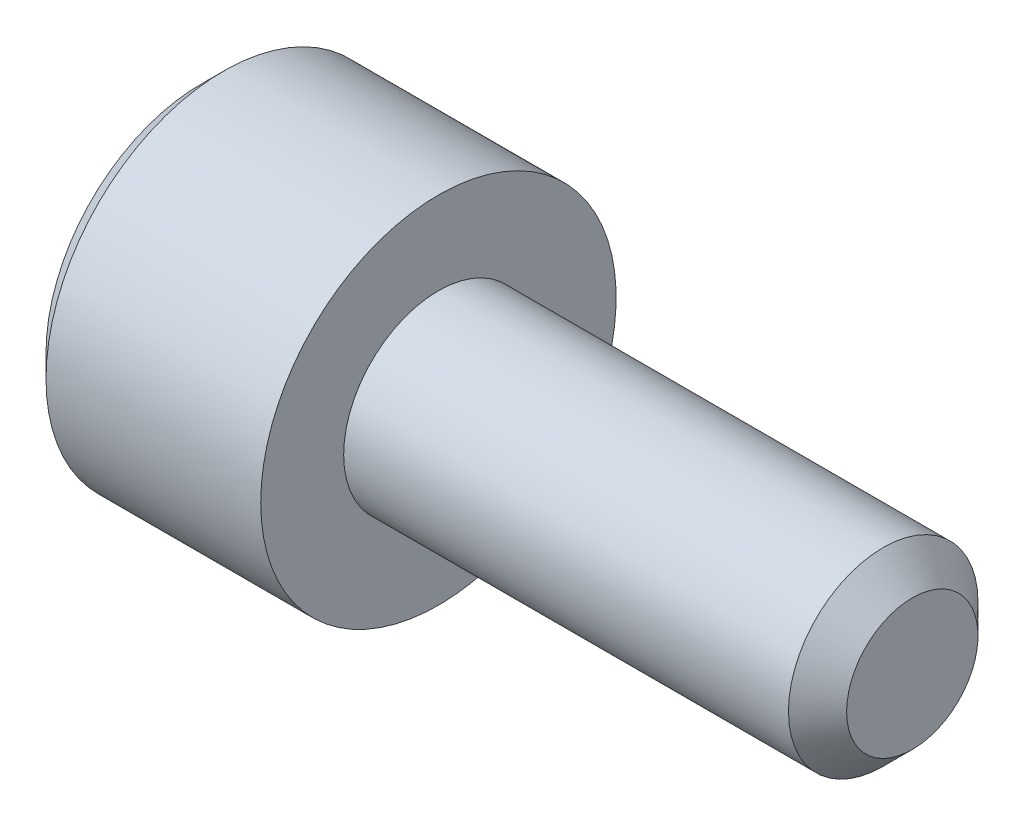
SolidWorks part; units mm, degrees
material "AISI 304"
ref_plane "正面" through (0, 0, 0) normal (0, 0, 1) x (1, 0, 0)
ref_plane "平面" through (0, 0, 0) normal (0, 1, 0) x (1, 0, 0)
ref_plane "右側面" through (0, 0, 0) normal (1, 0, 0) x (0, 0, -1)
ref_plane "Plane1" through (0, 0, 0) normal (0, 0, 1) x (1, 0, 0)
sketch "Sketch1" plane through (0, 0, 0) normal (0, 0, 1) x (1, 0, 0)
  line L0 (-2, 0) -> (-2, 1.3125)
  line L1 (-2, 1.3125) -> (-1.8125, 1.5)
  line L2 (-1.8125, 1.5) -> (0, 1.5)
  line L3 (0, 1.5) -> (0, 0.8)
  line L4 (0, 0.8) -> (3.7545, 0.8)
  line L5 (3.7545, 0.8) -> (4, 0.5545)
  line L6 (4, 0.5545) -> (4, 0)
  line L7 (4, 0) -> (-2, 0)
  line L8 (4, 0) -> (-2, 0) construction
  dimension "D1" = 0.8
revolve "Revolve1" add sketch "Sketch1" angle 360 about L8
cosmetic thread "Cosmetic Thread1" parameters "D1"=3.5, "D2"=1.509
ref_plane "Plane2" through (0, 0, 0) normal (0, 0, 1) x (1, 0, 0)
sketch "Sketch2" plane through (0, 0, 0) normal (0, 0, 1) x (1, 0, 0)
  line L0 (-2, 0) -> (-2, 0.9)
  line L1 (-2, 0.9) -> (-1.85, 0.75)
  line L2 (-1.85, 0.75) -> (-1, 0.75)
  line L3 (-1, 0.75) -> (-0.6, 0)
  line L4 (-0.6, 0) -> (-2, 0)
  line L5 (-0.6, 0) -> (-2, 0) construction
revolve "Cut-Revolve1" cut sketch "Sketch2" angle 360 about L5
ref_plane "Plane3" through (-2, 0, 0) normal (1, 0, 0) x (0, 0, -1)
sketch "Sketch3" plane through (-2, 0, 0) normal (1, 0, 0) x (0, 0, -1)
  line L0 (-0.75, -0.433) -> (0, -0.866)
  line L1 (0, -0.866) -> (0.75, -0.433)
  line L2 (0.75, -0.433) -> (0.75, 0.433)
  line L3 (0.75, 0.433) -> (0, 0.866)
  line L4 (0, 0.866) -> (-0.75, 0.433)
  line L5 (-0.75, 0.433) -> (-0.75, -0.433)
extrude "Cut-Extrude1" cut sketch "Sketch3" along normal blind 1
